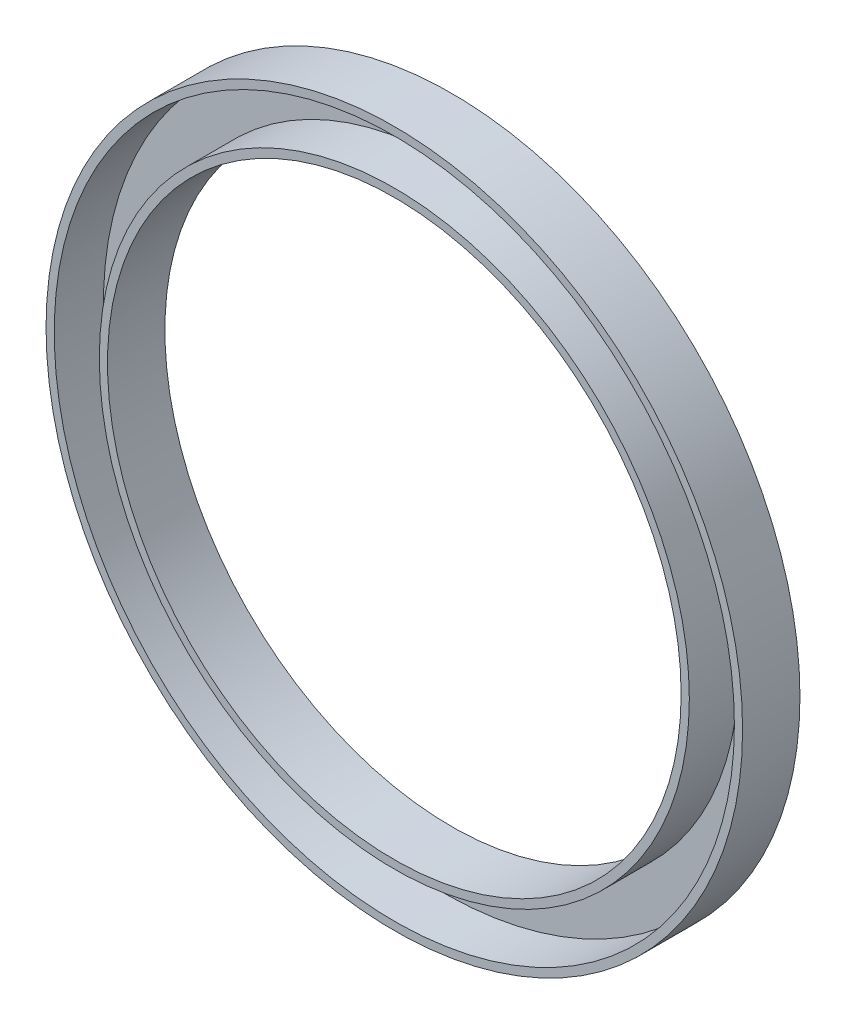
SolidWorks part; units mm, degrees
ref_plane "前视基准面" through (0, 0, 0) normal (0, 0, 1) x (1, 0, 0)
ref_plane "上视基准面" through (0, 0, 0) normal (0, 1, 0) x (1, 0, 0)
ref_plane "右视基准面" through (0, 0, 0) normal (1, 0, 0) x (0, 0, -1)
sketch "草图1" plane through (0, 0, 0) normal (0, 0, 1) x (1, 0, 0)
  circle A0 centre (0, 0) radius 85
  circle A1 centre (0, 0) radius 70
  dimension "D1" = 170
  dimension "D2" = 140
extrude "凸台-拉伸1" add sketch "草图1" along normal blind 14
shell "抽壳1" thickness 2
